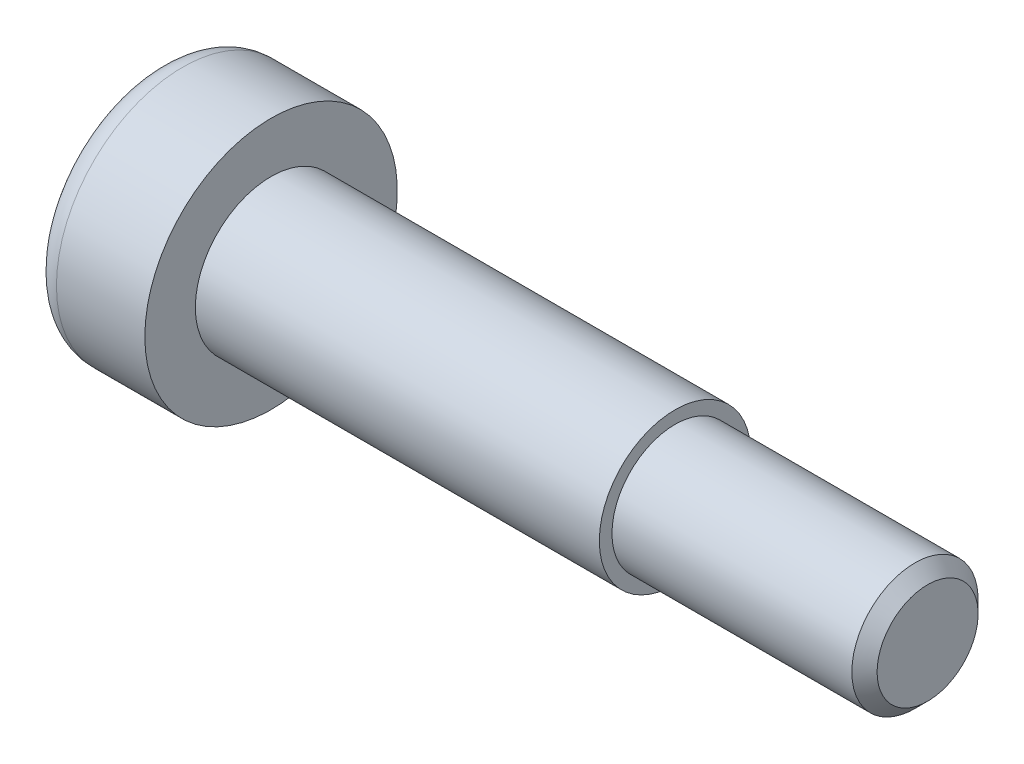
SolidWorks part; units mm, degrees
material "不锈钢 (铁素体)"
ref_plane "前视基准面" through (0, 0, 0) normal (0, 0, 1) x (1, 0, 0)
ref_plane "上视基准面" through (0, 0, 0) normal (0, 1, 0) x (1, 0, 0)
ref_plane "右视基准面" through (0, 0, 0) normal (1, 0, 0) x (0, 0, -1)
sketch "草图1" plane through (0, 0, 0) normal (0, 0, 1) x (1, 0, 0)
  line L0 (0, 0) -> (30.5, 0) construction
  line L1 (0, 0) -> (0, 5)
  line L2 (0, 5) -> (4.5, 5)
  line L3 (4.5, 5) -> (4.5, 3)
  line L4 (4.5, 3) -> (20.5, 3)
  line L5 (20.5, 3) -> (20.5, 2.5)
  line L6 (20.5, 2.5) -> (30.5, 2.5)
  line L7 (30.5, 2.5) -> (30.5, 0)
  line L8 (0, 0) -> (30.5, 0)
  dimension "D1" = 10
  dimension "D2" = 6
  dimension "D3" = 5
  dimension "D4" = 10
  dimension "D5" = 4.5
  dimension "D6" = 16
revolve "旋转1" add sketch "草图1" angle 360 about L0
cosmetic thread "装饰螺纹线1" parameters "D2"=4.134
sketch "草图2" plane through (0, 0, 0) normal (-1, 0, 0) x (0, 0, 1)
  line L0 (0, 0) -> (0, 1.7321) construction
  line L1 (0, 1.7321) -> (-1.5, 0.866)
  line L2 (-1.5, 0.866) -> (-1.5, -0.866)
  line L3 (-1.5, -0.866) -> (0, -1.7321)
  line L4 (0, -1.7321) -> (1.5, -0.866)
  line L5 (1.5, -0.866) -> (1.5, 0.866)
  line L6 (1.5, 0.866) -> (0, 1.7321)
  circle A0 centre (0, 0) radius 1.5 construction
  dimension "D1" = 3
extrude "切除-拉伸1" cut sketch "草图2" against normal blind 3
fillet "圆角1" radius 1 1 edges at (0, 0, 5)
chamfer "倒角1" distance 0.5 angle 45 1 edges at (30.5, 0, 2.5)
